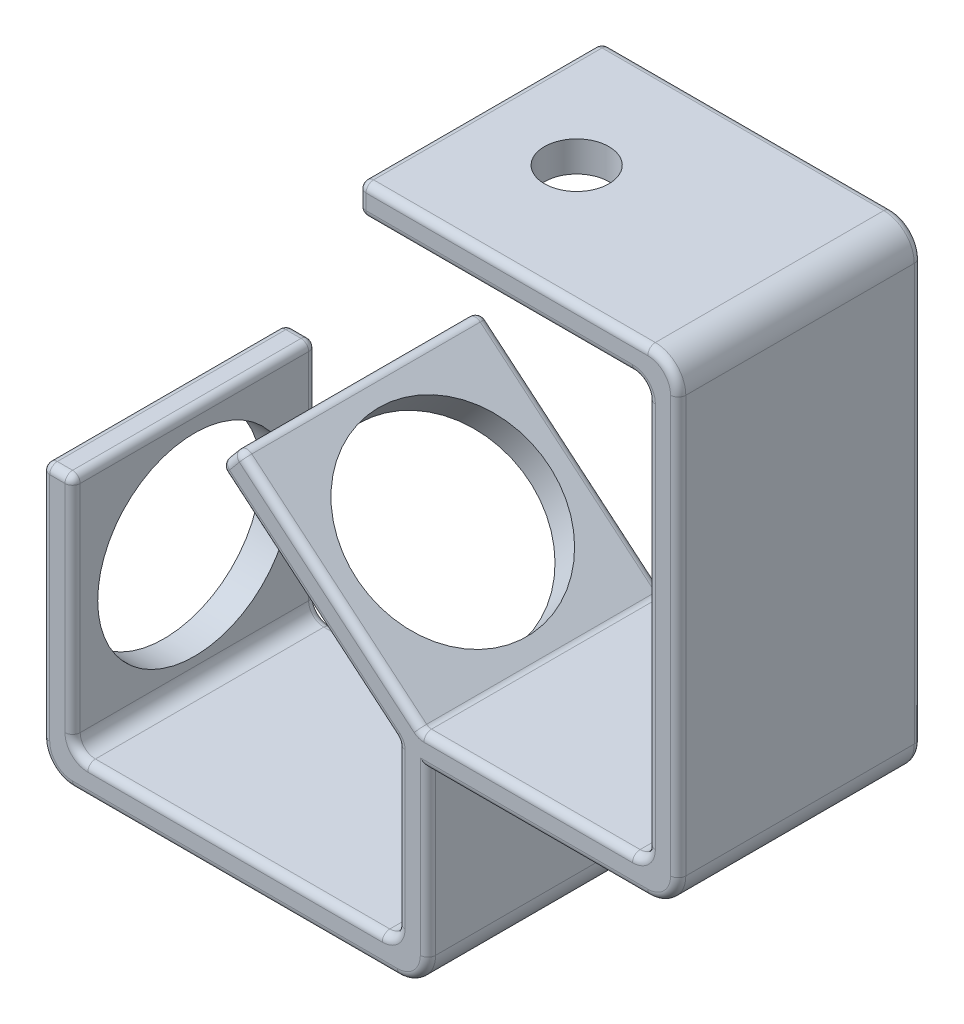
SolidWorks part; units mm, degrees
ref_plane "Front Plane" through (0, 0, 0) normal (0, 0, 1) x (1, 0, 0)
ref_plane "Top Plane" through (0, 0, 0) normal (0, 1, 0) x (1, 0, 0)
ref_plane "Right Plane" through (0, 0, 0) normal (1, 0, 0) x (0, 0, -1)
sketch "Sketch1" plane through (0, 0, 0) normal (0, 0, 1) x (1, 0, 0)
  line L0 (0, 53) -> (0, 0)
  line L1 (0, 0) -> (76, 0)
  line L2 (76, 0) -> (76, 38.2)
  line L4 (76, 38.2) -> (125.3, 38.2)
  line L5 (125.3, 38.2) -> (125.3, 132.2)
  line L6 (125.3, 132.2) -> (62.3, 132.2)
  dimension "D1" = 53
  dimension "D2" = 76
  dimension "D3" = 38.2
  dimension "D4" = 132.2
  dimension "D5" = 63
  dimension "D7" = 125.3
extrude "Extrude-Thin1" add sketch "Sketch1" against normal blind 48 thin thin type one direction reverse wall 6
sketch "Sketch2" plane through (0, 0, 0) normal (0, 0, 1) x (1, 0, 0)
  line L0 (70, 40.2838) -> (34.8064, 69.8148)
  line L1 (70, 6) -> (70, 44.2) construction
  line L2 (34.8064, 69.8148) -> (38.6631, 74.411)
  line L3 (38.6631, 74.411) -> (74.6672, 44.2)
  line L4 (70, 44.2) -> (119.3, 44.2) construction
  line L5 (74.6672, 44.2) -> (70, 44.2)
  line L6 (70, 44.2) -> (70, 40.2838)
  dimension "D1" = 47
  dimension "D2" = 6
  dimension "D3" = 3
  dimension "D4" = 130
extrude "Boss-Extrude1" add sketch "Sketch2" against normal blind 48 contours L2 L3 L5 L6 L0
sketch "Sketch3" plane through (0, 0, 0) normal (-1, 0, 0) x (0, 0, 1)
  circle A0 centre (-24, 29.8) radius 19.05
  dimension "D1" = 38.1
  dimension "D2" = 24
  dimension "D3" = 29.8
extrude "Cut-Extrude1" cut sketch "Sketch3" against normal up to surface (6 mm away) up to face at (6, 29.5, -24)
fillet "Fillet6" radius 3 4 edges at (119.3, 126.2, -24) (119.3, 44.2, -24) (70, 6, -24) (6, 6, -24)
fillet "Fillet7" radius 6 4 edges at (125.3, 132.2, -24) (125.3, 38.2, -24) (76, 0, -24) (0, 0, -24)
fillet "Fillet8" radius 1.5 58 edges at (6, 31, -48) (6.8787, 6.8787, -48) (70, 24.6419, -48) (69.1213, 6.8787, -48) (6, 31, 0) (6.8787, 6.8787, 0) (70, 24.6419, 0) (69.1213, 6.8787, 0) (38, 6, -48) (38, 6, 0) (0, 29.5, 0) (1.7574, 1.7574, 0) (76, 22.1, 0) (74.2426, 1.7574, 0) (0, 29.5, -48) (1.7574, 1.7574, -48) (76, 22.1, -48) (74.2426, 1.7574, -48) (97.65, 38.2, -48) (123.5426, 39.9574, -48) (125.3, 85.2, -48) (123.5426, 130.4426, -48) (97.65, 38.2, 0) (123.5426, 39.9574, 0) (125.3, 85.2, 0) (123.5426, 130.4426, 0) (89.3, 126.2, -48) (118.4213, 125.3213, -48) (119.3, 85.2, -48) (118.4213, 45.0787, -48) (89.3, 126.2, 0) (118.4213, 125.3213, 0) (119.3, 85.2, 0) (118.4213, 45.0787, 0) (70, 40.2838, -24) (52.4032, 55.0493, 0) (52.4032, 55.0493, -48) (56.6651, 59.3055, 0) (56.6651, 59.3055, -48) (62.3, 126.2, -24) (62.3, 129.2, -48) (62.3, 129.2, 0) (34.8064, 69.8148, -24) (36.7347, 72.1129, 0) (36.7347, 72.1129, -48) (38.6631, 74.411, -24) (0, 53, -24) (3, 53, -48) (6, 53, -24) (3, 53, 0) (38, 0, 0) (38, 0, -48) (62.3, 132.2, -24) (90.8, 132.2, -48) (90.8, 132.2, 0) (74.6672, 44.2, -24) (95.4836, 44.2, -48) (95.4836, 44.2, 0)
sketch "Sketch4" plane through (0, 132.2, 0) normal (0, 1, 0) x (1, 0, 0)
  line L0 (63.8, 48) -> (119.3, 48) construction
  line L1 (125.3, 46.5) -> (125.3, 1.5) construction
  circle A0 centre (81.3, 24) radius 6.35
  dimension "D1" = 12.7
  dimension "D2" = 24
  dimension "D3" = 44
extrude "Cut-Extrude2" cut sketch "Sketch4" against normal up to surface (6 mm away) up to face at (90.05, 126.2, -24)
sketch "Sketch5" plane through (52.6149, 62.704, 0) normal (0.6428, 0.766, 0) x (0.766, -0.6428, 0)
  line L0 (28.2412, 0) -> (-16.7128, 0) construction
  line L1 (-18.2128, 1.5) -> (-18.2128, 46.5) construction
  circle A0 centre (5.5872, 24) radius 19.05
  dimension "D1" = 38.1
  dimension "D2" = 24
  dimension "D3" = 23.8
extrude "Cut-Extrude3" cut sketch "Sketch5" against normal up to surface (6 mm away) up to face at (52.7098, 54.792, -24)
